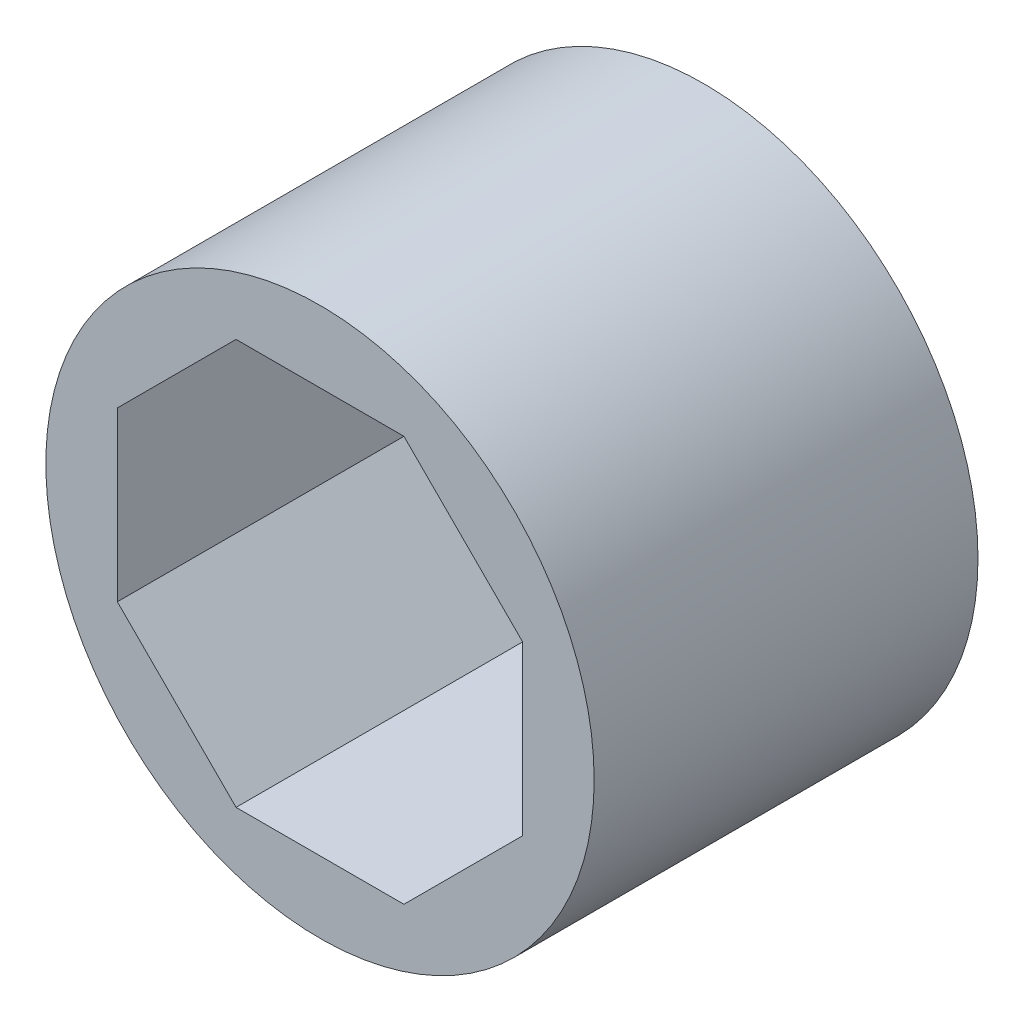
SolidWorks part; units mm, degrees
ref_plane "Front Plane" through (0, 0, 0) normal (0, 0, 1) x (1, 0, 0)
ref_plane "Top Plane" through (0, 0, 0) normal (0, 1, 0) x (1, 0, 0)
ref_plane "Right Plane" through (0, 0, 0) normal (1, 0, 0) x (0, 0, -1)
sketch "Sketch2" plane through (0, 0, 0) normal (0, 0, 1) x (1, 0, 0)
  line L1 (1.5307, 3.6955) -> (-1.5307, 3.6955)
  line L2 (-1.5307, 3.6955) -> (-3.6955, 1.5307)
  line L3 (-3.6955, 1.5307) -> (-3.6955, -1.5307)
  line L4 (-3.6955, -1.5307) -> (-1.5307, -3.6955)
  line L5 (-1.5307, -3.6955) -> (1.5307, -3.6955)
  line L6 (1.5307, -3.6955) -> (3.6955, -1.5307)
  line L7 (3.6955, -1.5307) -> (3.6955, 1.5307)
  line L8 (3.6955, 1.5307) -> (1.5307, 3.6955)
  circle A0 centre (0, 0) radius 4 construction
  circle A1 centre (0, 0) radius 3.6955 construction
  circle A2 centre (0, 0) radius 5
  dimension "D1" = 8
  dimension "D2" = 10
extrude "Boss-Extrude1" add sketch "Sketch2" along normal blind 7
